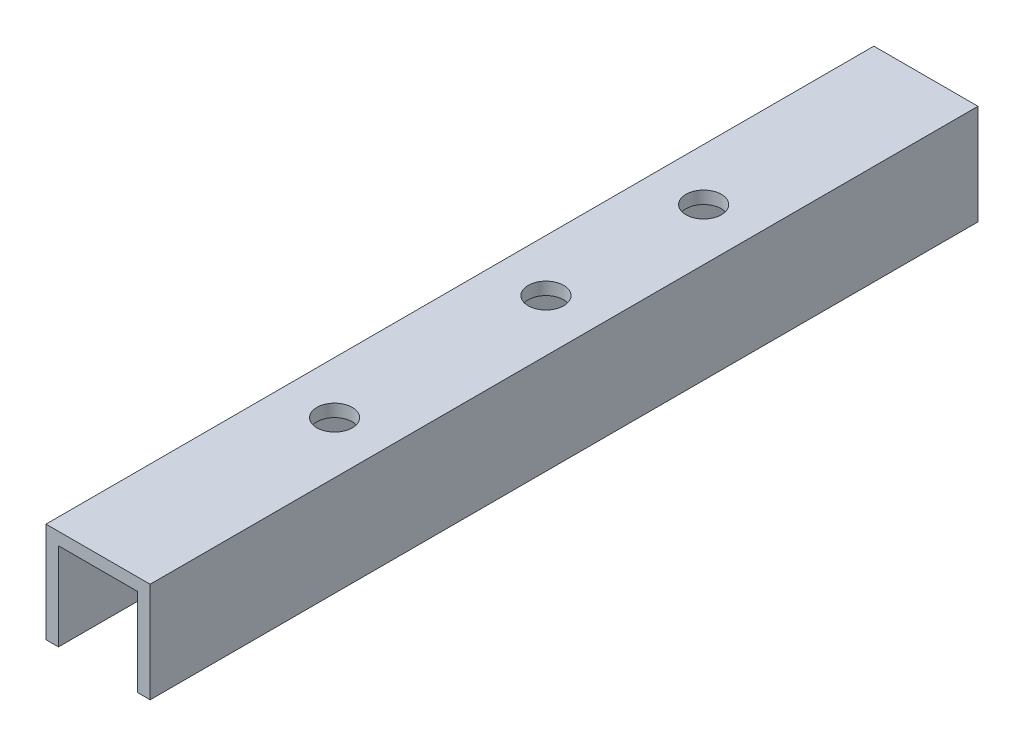
SolidWorks part; units mm, degrees
ref_plane "Front Plane" through (0, 0, 0) normal (0, 0, 1) x (1, 0, 0)
ref_plane "Top Plane" through (0, 0, 0) normal (0, 1, 0) x (1, 0, 0)
ref_plane "Right Plane" through (0, 0, 0) normal (1, 0, 0) x (0, 0, -1)
sketch "Sketch1" plane through (0, 0, 0) normal (0, 0, 1) x (1, 0, 0)
  line L0 (0, 0) -> (0, -1.5875) construction
  line L1 (-6.604, 0) -> (6.604, 0)
  line L2 (6.604, 0) -> (6.604, -12.7)
  line L3 (6.604, -12.7) -> (5.0165, -12.7)
  line L4 (5.0165, -12.7) -> (5.0165, -1.5875)
  line L5 (5.0165, -1.5875) -> (-5.0165, -1.5875)
  line L6 (-5.0165, -12.7) -> (-5.0165, -1.5875)
  line L7 (-6.604, -12.7) -> (-5.0165, -12.7)
  line L8 (-6.604, 0) -> (-6.604, -12.7)
  dimension "D1" = 12.7
  dimension "D2" = 1.5875
  dimension "D3" = 13.208
extrude "Boss-Extrude1" add sketch "Sketch1" against normal blind 105
hole_wizard "M4 Clearance Hole2" positions "Sketch4" profile "Sketch5" hole size "M4" standard "ANSI Metric" end condition through all
sketch "Sketch4" plane through (0, 0, 0) normal (0, 1, 0) x (1, 0, 0)
  line L0 (6.604, 0) -> (-6.604, 0) construction
  point P9 (0, 30)
  point P16 (0, 76.8078)
  point P18 (0, 56.8078)
  dimension "D3" = 20
  dimension "D1" = 30
  dimension "D2" = 26.8078
sketch "Sketch5" plane through (0, 0, -56.8078) normal (1, 0, 0) x (0, 0, 1)
  line L0 (0, 0) -> (0, 12.7)
  line L1 (0, 12.7) -> (2.25, 12.7)
  line L2 (2.25, 12.7) -> (2.25, 0)
  line L5 (2.25, 0) -> (0, 0)
  line L11 (0, -6.35) -> (0, 107.95) construction
  dimension "Thru Hole Dia." = 4.5
  dimension "Thru Hole Depth" = 12.7
